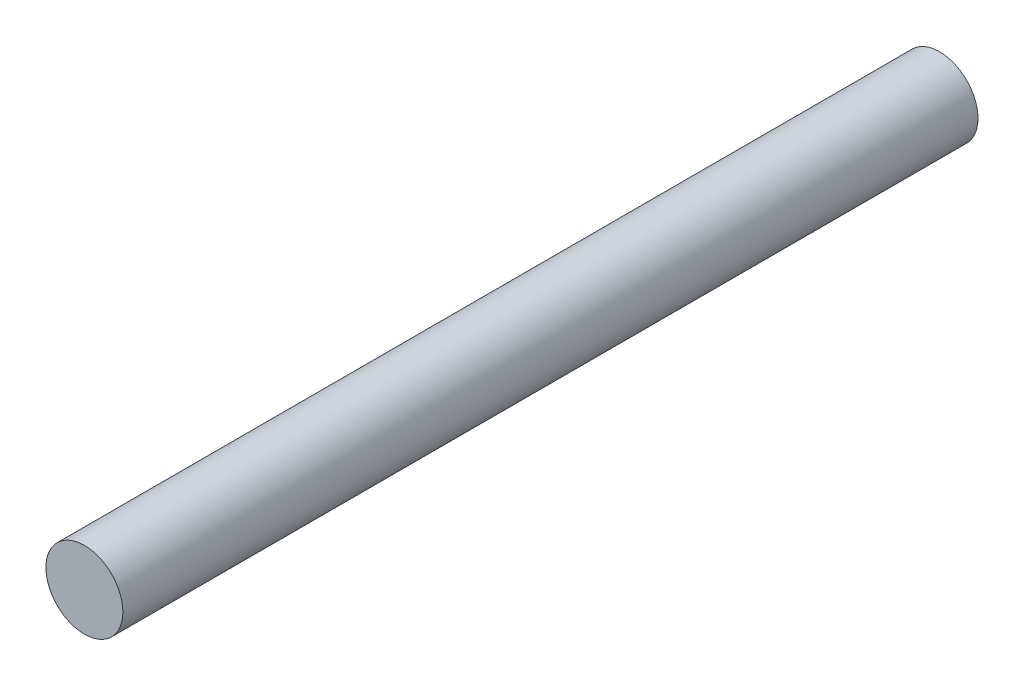
SolidWorks part; units mm, degrees
ref_plane "Front Plane" through (0, 0, 0) normal (0, 0, 1) x (1, 0, 0)
ref_plane "Top Plane" through (0, 0, 0) normal (0, 1, 0) x (1, 0, 0)
ref_plane "Right Plane" through (0, 0, 0) normal (1, 0, 0) x (0, 0, -1)
sketch "Sketch1" plane through (0, 0, 0) normal (0, 0, 1) x (1, 0, 0)
  circle A0 centre (0, 0) radius 4.5
  dimension "D1" = 9
extrude "Boss-Extrude1" add sketch "Sketch1" along normal blind 100
sketch "Sketch2" plane through (0, 0, 100) normal (0, 0, 1) x (1, 0, 0)
  point P0 (0, 0)
  point P3 (0, 0)
sketch "Sketch3" plane through (0, 0, 0) normal (0, 0, -1) x (-1, 0, 0)
  point P0 (0, 0)
